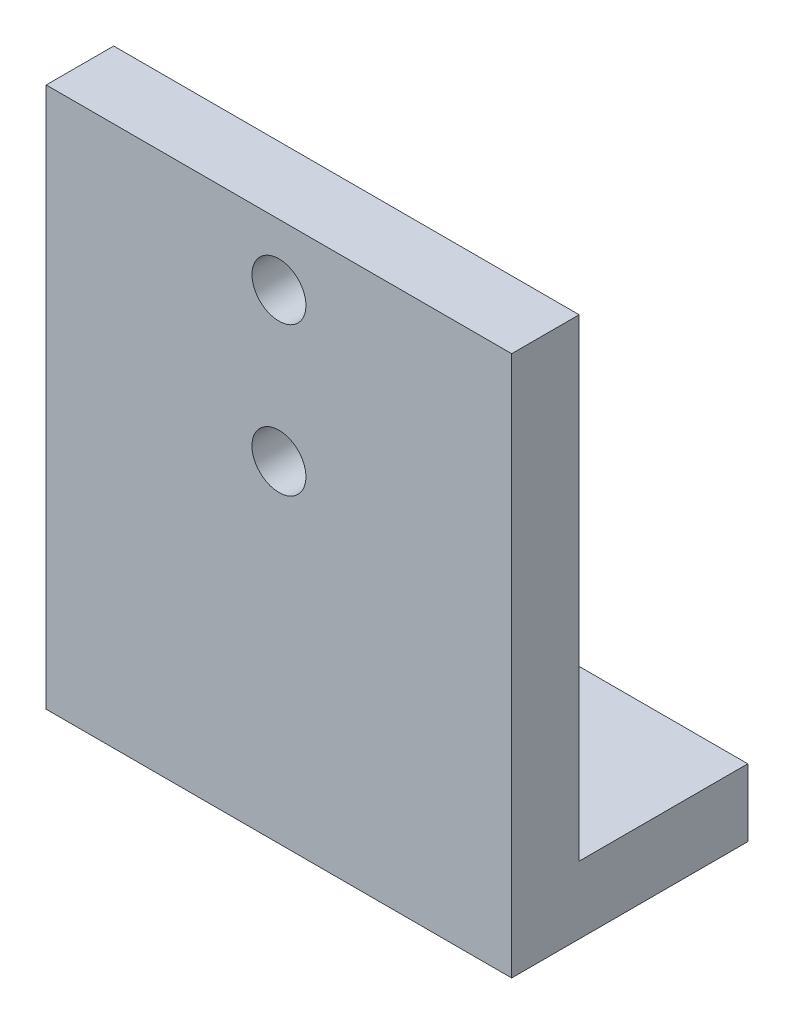
SolidWorks part; units mm, degrees
ref_plane "Front Plane" through (0, 0, 0) normal (0, 0, 1) x (1, 0, 0)
ref_plane "Top Plane" through (0, 0, 0) normal (0, 1, 0) x (1, 0, 0)
ref_plane "Right Plane" through (0, 0, 0) normal (1, 0, 0) x (0, 0, -1)
sketch "Sketch1" plane through (0, 0, 0) normal (1, 0, 0) x (0, 0, -1)
  line L0 (0, 80.15) -> (0, 0)
  line L1 (0, 0) -> (35, 0)
  line L2 (35, 0) -> (35, 10)
  line L3 (35, 10) -> (10, 10)
  line L4 (10, 10) -> (10, 80.15)
  line L5 (10, 80.15) -> (0, 80.15)
  dimension "D1" = 80.15
  dimension "D2" = 10
  dimension "D3" = 10
  dimension "D4" = 35
extrude "Boss-Extrude1" add sketch "Sketch1" along normal blind 69
sketch "Sketch2" plane through (0, 0, -10) normal (0, 0, -1) x (-1, 0, 0)
  line L0 (-34.5, 80.15) -> (-34.5, 10) construction
  line L1 (-69, 80.15) -> (0, 80.15) construction
  line L2 (-69, 10) -> (0, 10) construction
  circle A0 centre (-34.5, 71.08) radius 4
  circle A1 centre (-34.5, 49.08) radius 4
  dimension "D1" = 8
  dimension "D3" = 8
  dimension "D4" = 22
  dimension "D2" = 9.07
extrude "Cut-Extrude1" cut sketch "Sketch2" against normal through all
sketch "Sketch3" plane through (0, 10, 0) normal (0, 1, 0) x (1, 0, 0)
  line L0 (0, 22.5) -> (69, 22.5) construction
  line L1 (0, 35) -> (0, 10) construction
  line L2 (69, 35) -> (69, 10) construction
  line L3 (34.5, 35) -> (34.5, 10) construction
  line L4 (69, 35) -> (0, 35) construction
  line L5 (69, 10) -> (0, 10) construction
  line L6 (0, 10) -> (34.5, 22.5) construction
  line L7 (34.5, 22.5) -> (69, 35) construction
  line L8 (0, 35) -> (34.5, 22.5) construction
  line L9 (34.5, 22.5) -> (69, 10) construction
  circle A0 centre (17, 22.5) radius 3
  circle A1 centre (52, 22.5) radius 3
  dimension "D1" = 17.5
  dimension "D2" = 6
extrude "Cut-Extrude2" cut sketch "Sketch3" against normal blind 10
